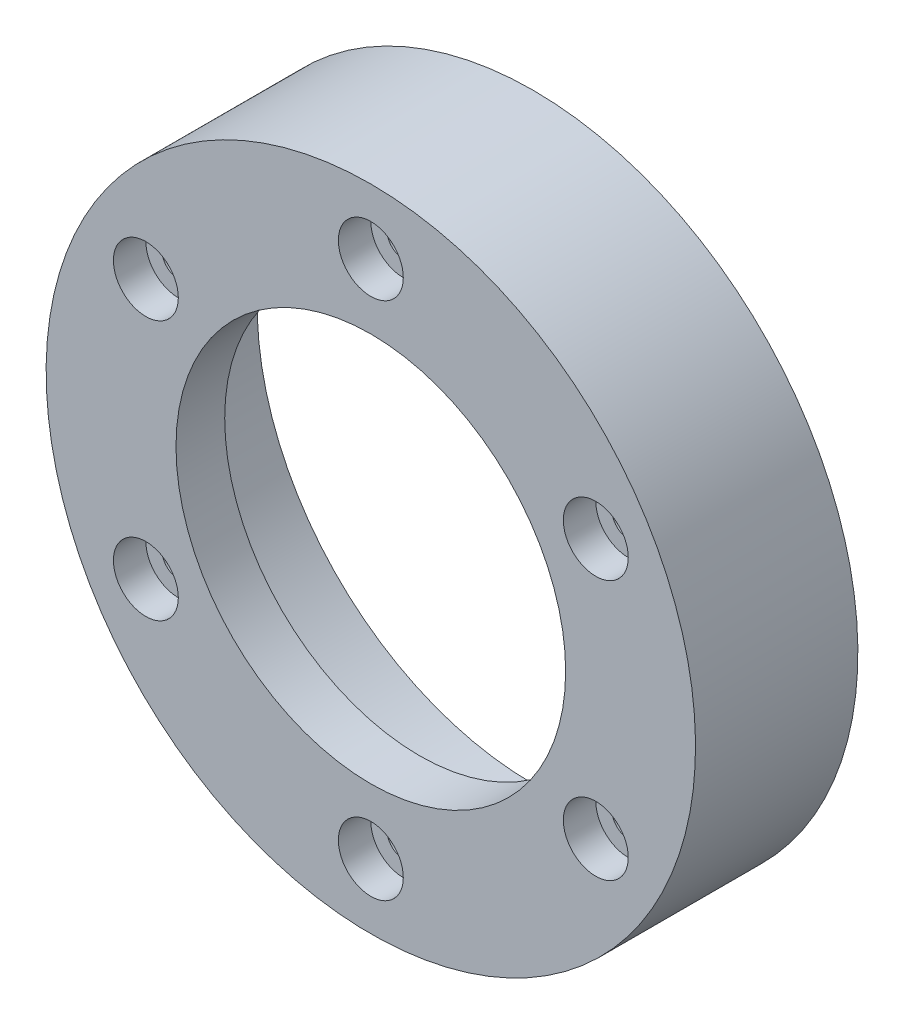
SolidWorks part; units mm, degrees
material "Brass"
ref_plane "Front Plane" through (0, 0, 0) normal (0, 0, 1) x (1, 0, 0)
ref_plane "Top Plane" through (0, 0, 0) normal (0, 1, 0) x (1, 0, 0)
ref_plane "Right Plane" through (0, 0, 0) normal (1, 0, 0) x (0, 0, -1)
sketch "Sketch1" plane through (0, 0, 0) normal (1, 0, 0) x (0, 0, -1)
  line L0 (7.9375, 0) -> (-7.9375, 0) construction
  line L1 (-7.9375, 0) -> (-7.9375, 31.75) construction
  line L2 (-7.9375, 31.75) -> (7.9375, 31.75)
  line L3 (7.9375, 31.75) -> (7.9375, 26.9875)
  line L4 (7.9375, 26.9875) -> (-3.175, 26.9875)
  line L5 (-3.175, 26.9875) -> (-3.175, 19.05)
  line L6 (-3.175, 19.05) -> (-7.9375, 19.05)
  line L7 (7.9375, 31.75) -> (7.9375, 0) construction
  line L8 (-7.9375, 31.75) -> (-7.9375, 19.05)
  point P4 (0, 0)
  dimension "D1" = 38.1
  dimension "D2" = 53.975
  dimension "D3" = 63.5
  dimension "D4" = 15.875
  dimension "D5" = 4.7625
revolve "Revolve1" add sketch "Sketch1" angle 360 about L0
hole_wizard "CBORE for #0 Binding Head Machine Screw1" positions "Sketch2" profile "Sketch3" counterbore size "#0" standard "ANSI Inch" end condition through all
sketch "Sketch2" plane through (0, 0, 7.9375) normal (0, 0, 1) x (1, 0, 0)
  line L0 (0, 25.4) -> (0, -25.4) construction
  point P0 (0, 25.4)
  point P6 (21.997, 12.7)
  point P7 (21.997, -12.7)
  point P8 (0, -25.4)
  point P9 (-21.997, -12.7)
  point P10 (-21.997, 12.7)
  dimension "D2" = 50.8
  dimension "D1" = 6
sketch "Sketch3" plane through (0, 25.4, 7.9375) normal (1, 0, 0) x (0, -1, 0)
  line L0 (0, 0) -> (0, 15.875)
  line L1 (0, 15.875) -> (1.5875, 15.875)
  line L3 (1.5875, 15.875) -> (1.5875, 3.175)
  line L4 (1.5875, 3.175) -> (3.175, 3.175)
  line L5 (3.175, 3.175) -> (3.175, 0)
  line L7 (3.175, 0) -> (0, 0)
  line L11 (0, -6.35) -> (0, 107.95) construction
  dimension "Thru Hole Dia." = 3.175
  dimension "Thru Hole Depth" = 15.875
  dimension "C'Bore Dia." = 6.35
  dimension "C'Bore Depth" = 3.175
